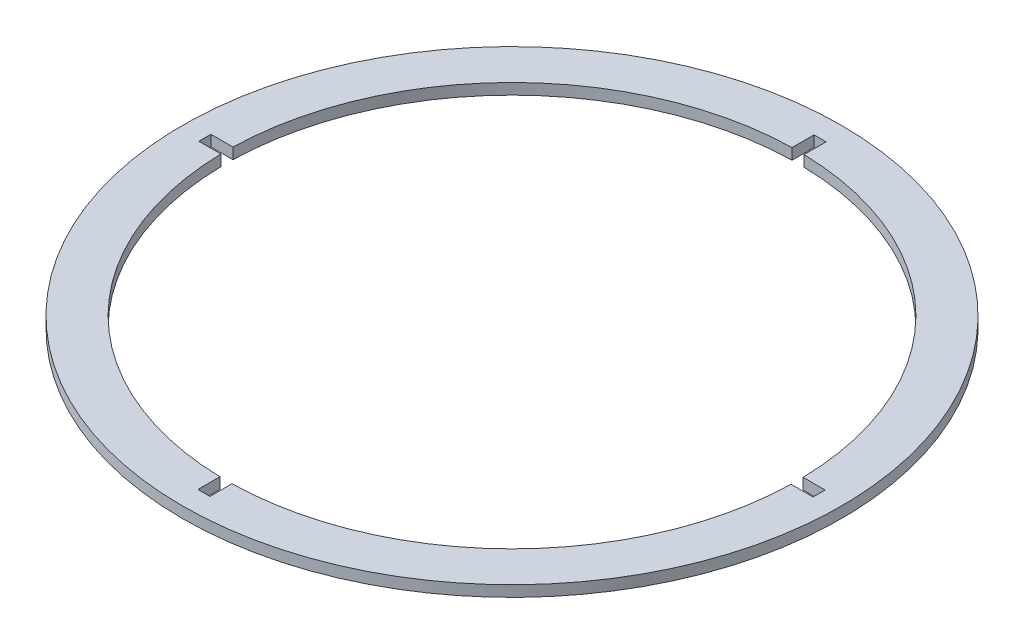
SolidWorks part; units mm, degrees
ref_plane "Front Plane" through (0, 0, 0) normal (0, 0, 1) x (1, 0, 0)
ref_plane "Top Plane" through (0, 0, 0) normal (0, 1, 0) x (1, 0, 0)
ref_plane "Right Plane" through (0, 0, 0) normal (1, 0, 0) x (0, 0, -1)
sketch "Sketch1" plane through (0, 0, 0) normal (0, 1, 0) x (1, 0, 0)
  line L0 (2.525, -129.9755) -> (2.525, -140)
  line L1 (2.525, -140) -> (-2.975, -140)
  line L2 (-2.975, -140) -> (-2.975, -129.966)
  line L3 (-129.9755, -2.525) -> (-140, -2.525)
  line L4 (-140, -2.525) -> (-140, 2.975)
  line L5 (-140, 2.975) -> (-129.966, 2.975)
  line L6 (-2.525, 129.9755) -> (-2.525, 140)
  line L7 (-2.525, 140) -> (2.975, 140)
  line L8 (2.975, 140) -> (2.975, 129.966)
  line L12 (129.9755, 2.525) -> (140, 2.525)
  line L13 (140, 2.525) -> (140, -2.975)
  line L14 (140, -2.975) -> (129.966, -2.975)
  arc A0 (-2.525, 129.9755) -> (-129.966, 2.975) centre (0, 0) ccw
  arc A1 (-129.9755, -2.525) -> (-2.975, -129.966) centre (0, 0) ccw
  circle A2 centre (0, 0) radius 150
  arc A3 (129.9755, 2.525) -> (2.975, 129.966) centre (0, 0) ccw
  arc A4 (2.525, -129.9755) -> (129.966, -2.975) centre (0, 0) ccw
  point P4 (130, 0)
  point P24 (0, 0)
  point P31 (0, 0)
  point P33 (150, 0)
  dimension "D2" = 260
  dimension "D6" = 300
  dimension "D3" = 10
  dimension "D4" = 4
  dimension "D7" = 5.5
  dimension "D8" = 2.525
extrude "Boss-Extrude1" add sketch "Sketch1" along normal mid plane 5
